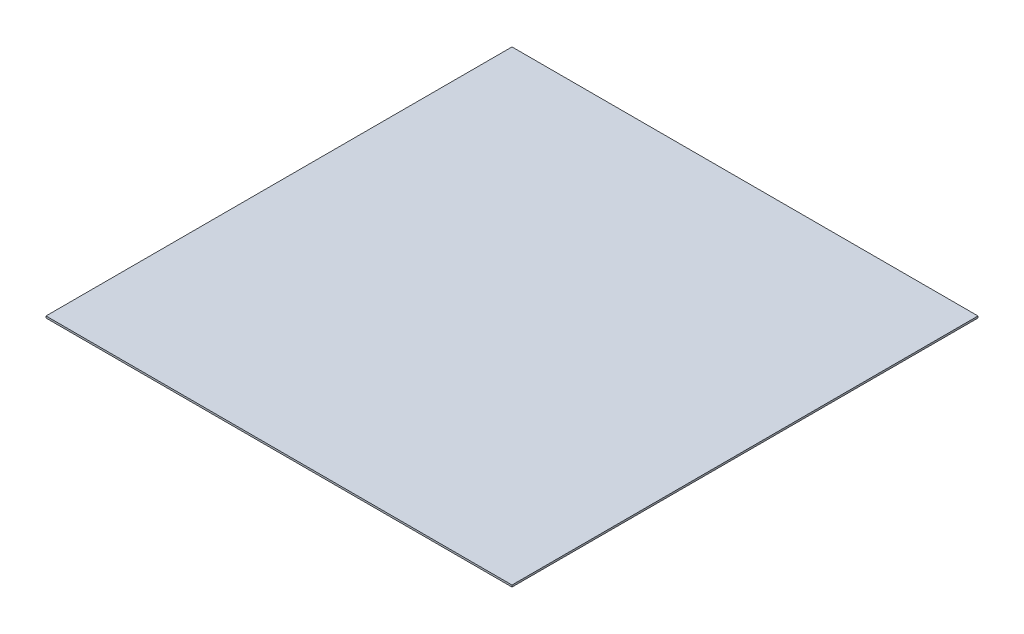
SolidWorks part; units mm, degrees
ref_plane "Front Plane" through (0, 0, 0) normal (0, 0, 1) x (1, 0, 0)
ref_plane "Top Plane" through (0, 0, 0) normal (0, 1, 0) x (1, 0, 0)
ref_plane "Right Plane" through (0, 0, 0) normal (1, 0, 0) x (0, 0, -1)
sketch "Sketch1" plane through (0, 0, 0) normal (0, 1, 0) x (1, 0, 0)
  line L1 (-255, -255) -> (255, -255)
  line L2 (-255, -255) -> (-255, 255)
  line L3 (-255, 255) -> (255, 255)
  line L4 (255, -255) -> (255, 255)
  line L5 (-255, -255) -> (255, 255) construction
  line L6 (-255, 255) -> (255, -255) construction
  point P0 (0, 0)
  dimension "D1" = 510
  dimension "D2" = 510
extrude "Boss-Extrude1" add sketch "Sketch1" along normal blind 2
